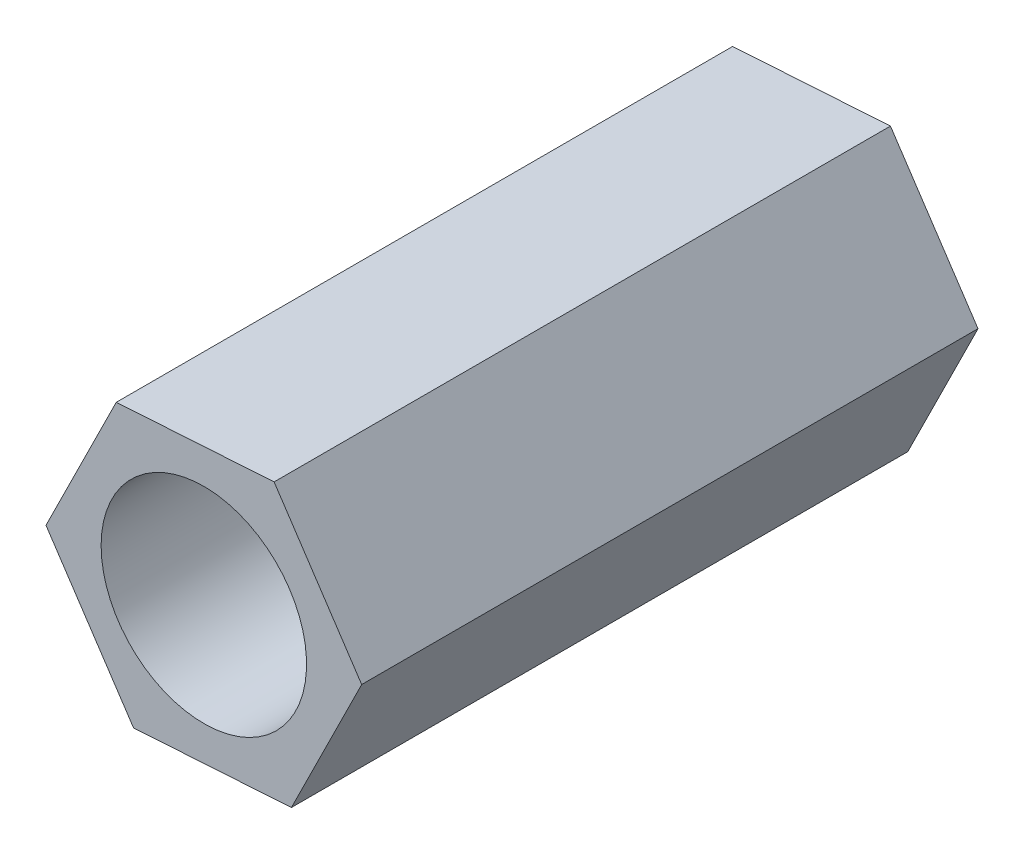
SolidWorks part; units mm, degrees
ref_plane "前视基准面" through (0, 0, 0) normal (0, 0, 1) x (1, 0, 0)
ref_plane "上视基准面" through (0, 0, 0) normal (0, 1, 0) x (1, 0, 0)
ref_plane "右视基准面" through (0, 0, 0) normal (1, 0, 0) x (0, 0, -1)
sketch "草图1" plane through (0, 0, 0) normal (0, 0, 1) x (1, 0, 0)
  line L1 (1.0263, 2.0688) -> (-1.2785, 1.9232)
  line L2 (-1.2785, 1.9232) -> (-2.3048, -0.1456)
  line L3 (-2.3048, -0.1456) -> (-1.0263, -2.0688)
  line L4 (-1.0263, -2.0688) -> (1.2785, -1.9232)
  line L5 (1.2785, -1.9232) -> (2.3048, 0.1456)
  line L6 (2.3048, 0.1456) -> (1.0263, 2.0688)
  circle A0 centre (0, 0) radius 2 construction
  dimension "D1" = 4
extrude "凸台-拉伸1" add sketch "草图1" along normal blind 9
sketch "草图2" plane through (0, 0, 0) normal (0, 0, -1) x (-1, 0, 0)
  circle A0 centre (0, 0) radius 1.5
  dimension "D1" = 3
extrude "切除-拉伸1" cut sketch "草图2" against normal through all
